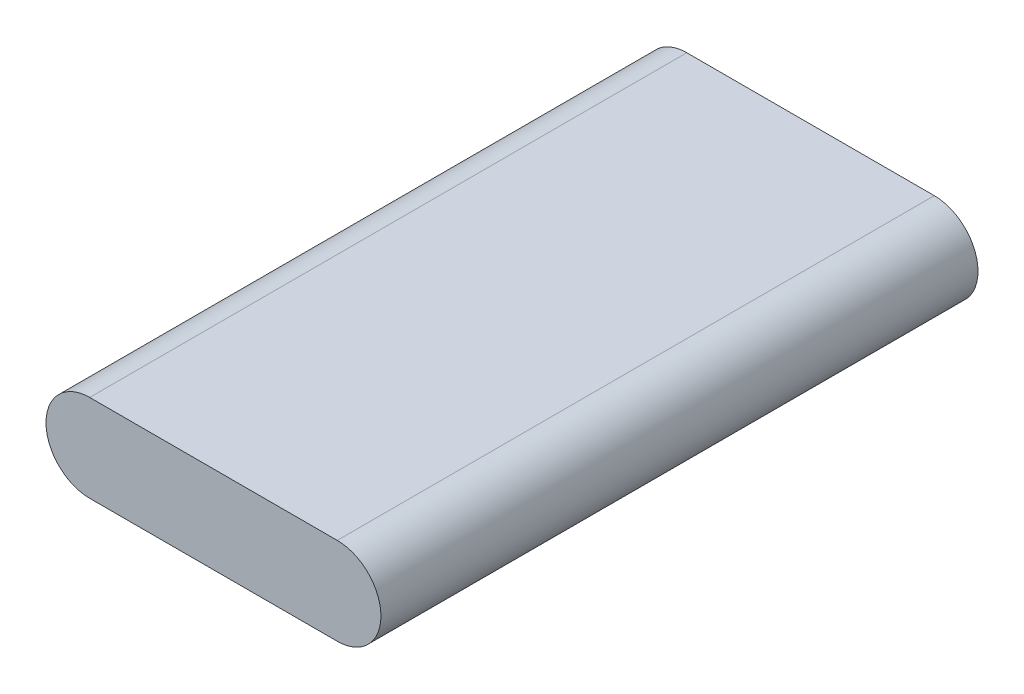
SolidWorks part; units mm, degrees
ref_plane "Front Plane" through (0, 0, 0) normal (0, 0, 1) x (1, 0, 0)
ref_plane "Top Plane" through (0, 0, 0) normal (0, 1, 0) x (1, 0, 0)
ref_plane "Right Plane" through (0, 0, 0) normal (1, 0, 0) x (0, 0, -1)
sketch "Sketch1" plane through (0, 0, 0) normal (0, 0, 1) x (1, 0, 0)
  line L1 (0, 15.24) -> (43.18, 15.24)
  line L2 (0, 15.24) -> (0, 0) construction
  line L3 (0, 0) -> (43.18, 0)
  line L4 (43.18, 15.24) -> (43.18, 0) construction
  arc A0 (0, 15.24) -> (0, 0) centre (0, 7.62) ccw
  arc A1 (43.18, 15.24) -> (43.18, 0) centre (43.18, 7.62) cw
  point P0 (50.8, 7.62)
  point P1 (-7.62, 7.62)
  dimension "D1" = 15.24
  dimension "D2" = 58.42
extrude "Boss-Extrude1" add sketch "Sketch1" along normal blind 104.14
